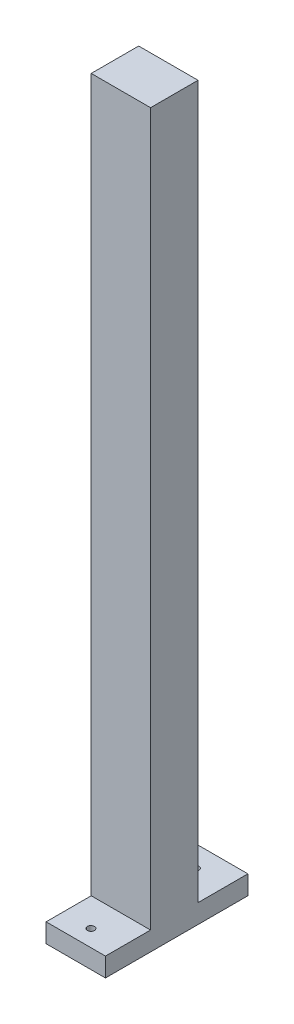
SolidWorks part; units mm, degrees
ref_plane "Front Plane" through (0, 0, 0) normal (0, 0, 1) x (1, 0, 0)
ref_plane "Top Plane" through (0, 0, 0) normal (0, 1, 0) x (1, 0, 0)
ref_plane "Right Plane" through (0, 0, 0) normal (1, 0, 0) x (0, 0, -1)
sketch "Sketch2" plane through (0, 0, 0) normal (1, 0, 0) x (0, 0, -1)
  line L0 (-10, 8) -> (-10, 308)
  line L1 (-29, 8) -> (-10, 8)
  line L2 (-29, 8) -> (-29, 0)
  line L3 (-29, 0) -> (31, 0)
  line L4 (31, 8) -> (31, 0)
  line L5 (-10, 308) -> (10, 308)
  line L6 (10, 308) -> (10, 8)
  line L7 (10, 8) -> (31, 8)
  line L8 (0, 41.365) -> (0, -28.7834) construction
  dimension "D1" = 60
  dimension "D2" = 20
  dimension "D3" = 10
  dimension "D4" = 21
  dimension "D5" = 8
  dimension "D6" = 300
extrude "Boss-Extrude1" add sketch "Sketch2" along normal blind 15 and the other way blind 10
sketch "Sketch3" plane through (0, 8, 0) normal (0, 1, 0) x (1, 0, 0)
  line L0 (-10, -10) -> (15, -10) construction
  circle A0 centre (1.8633, -22) radius 1.5
  dimension "D1" = 3
  dimension "12" = 12
extrude "Cut-Extrude2" cut sketch "Sketch3" against normal through all
mirror "Mirror2" about plane through (0, 0, 0) normal (0, 0, 1) of "Cut-Extrude2"
